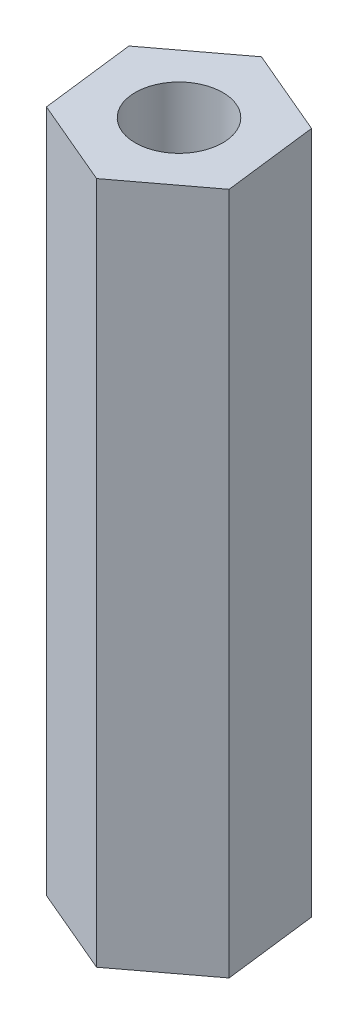
SolidWorks part; units mm, degrees
material "黄铜"
ref_plane "前视基准面" through (0, 0, 0) normal (0, 0, 1) x (1, 0, 0)
ref_plane "上视基准面" through (0, 0, 0) normal (0, 1, 0) x (1, 0, 0)
ref_plane "右视基准面" through (0, 0, 0) normal (1, 0, 0) x (0, 0, -1)
sketch "草图1" plane through (0, 0, 0) normal (0, 1, 0) x (1, 0, 0)
  line L1 (2.7672, 2.0839) -> (-0.4211, 3.4384)
  line L2 (-0.4211, 3.4384) -> (-3.1883, 1.3545)
  line L3 (-3.1883, 1.3545) -> (-2.7672, -2.0839)
  line L4 (-2.7672, -2.0839) -> (0.4211, -3.4384)
  line L5 (0.4211, -3.4384) -> (3.1883, -1.3545)
  line L6 (3.1883, -1.3545) -> (2.7672, 2.0839)
  circle A0 centre (0, 0) radius 1.6
  circle A1 centre (0, 0) radius 3 construction
  dimension "D1" = 3.2
extrude "凸台-拉伸1" add sketch "草图1" along normal blind 25
